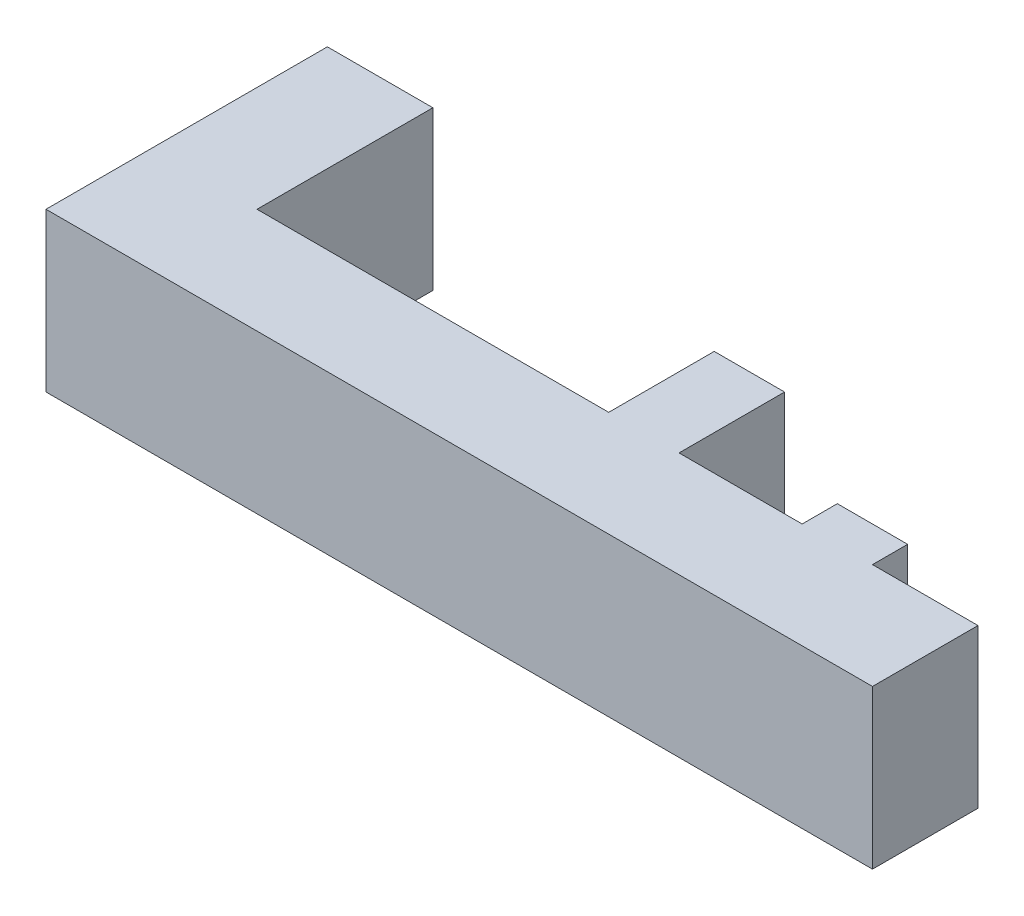
SolidWorks part; units mm, degrees
ref_plane "Alzado" through (0, 0, 0) normal (0, 0, 1) x (1, 0, 0)
ref_plane "Planta" through (0, 0, 0) normal (0, 1, 0) x (1, 0, 0)
ref_plane "Vista lateral" through (0, 0, 0) normal (1, 0, 0) x (0, 0, -1)
sketch "Croquis1" plane through (0, 0, 0) normal (0, 1, 0) x (1, 0, 0)
  line L0 (13, 6) -> (13, 3)
  line L1 (13, 6) -> (15, 6)
  line L2 (15, 6) -> (15, 3)
  line L3 (15, 3) -> (18.5, 3)
  line L4 (18.5, 3) -> (18.5, 4)
  line L5 (18.5, 4) -> (20.5, 4)
  line L6 (13, 3) -> (3, 3)
  line L7 (0, 0) -> (23.5, 0)
  line L8 (3, 3) -> (3, 8)
  line L9 (20.5, 4) -> (20.5, 3)
  line L10 (20.5, 3) -> (23.5, 3)
  line L11 (23.5, 3) -> (23.5, 0)
  line L12 (3, 8) -> (0, 8)
  line L13 (0, 8) -> (0, 0)
  dimension "D1" = 2
  dimension "D2" = 2
  dimension "D3" = 3.5
  dimension "D4" = 1
  dimension "D5" = 3
  dimension "D6" = 3
  dimension "D7" = 5
  dimension "D8" = 3
  dimension "D9" = 10
  dimension "D10" = 5
extrude "Saliente-Extruir1" add sketch "Croquis1" along normal blind 4.5
